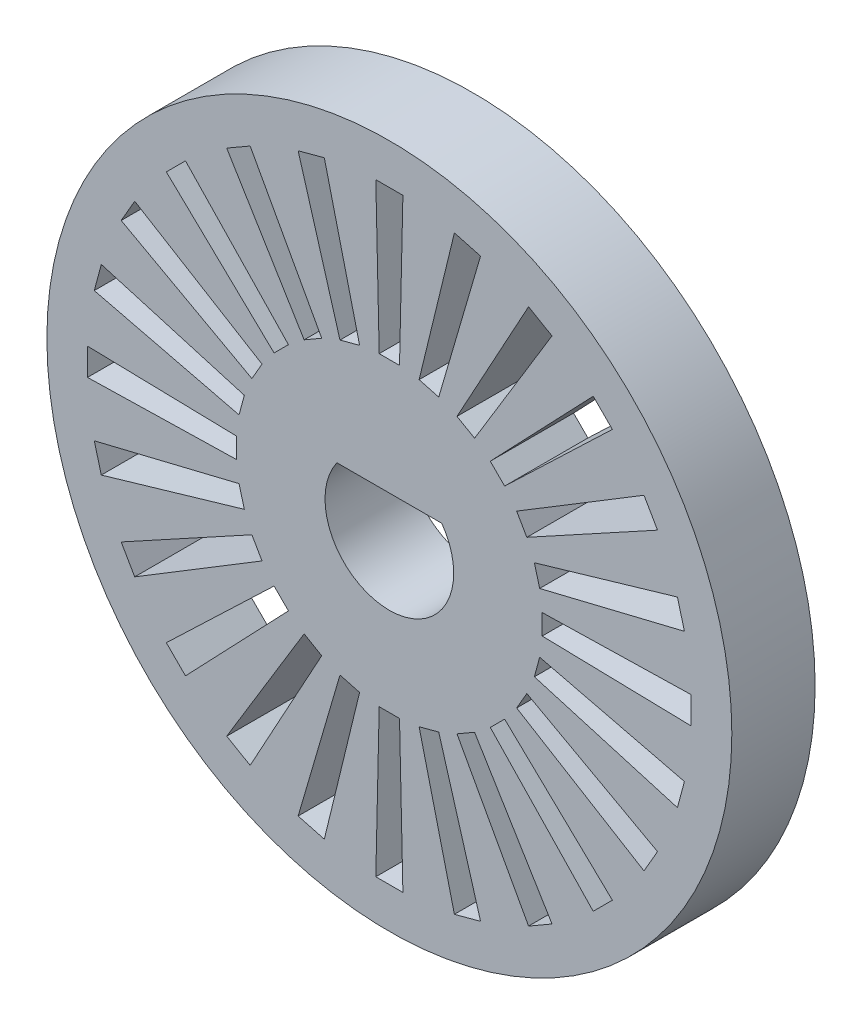
SolidWorks part; units mm, degrees
ref_plane "Alzado" through (0, 0, 0) normal (0, 0, 1) x (1, 0, 0)
ref_plane "Planta" through (0, 0, 0) normal (0, 1, 0) x (1, 0, 0)
ref_plane "Vista lateral" through (0, 0, 0) normal (1, 0, 0) x (0, 0, -1)
sketch "Croquis1" plane through (0, 0, 0) normal (0, 0, 1) x (1, 0, 0)
  line L0 (0, 12.8461) -> (0, 2.413) construction
  line L1 (0.508, 5.734) -> (-0.508, 5.734)
  line L2 (0.508, 5.734) -> (0.508, 11.3221)
  line L3 (0.508, 11.3221) -> (-0.508, 11.3221)
  line L4 (-0.508, 5.734) -> (-0.508, 11.3221)
  line L5 (0.508, 5.734) -> (-0.508, 11.3221) construction
  line L6 (0.508, 11.3221) -> (-0.508, 5.734) construction
  line L7 (-0.508, 11.3221) -> (-0.381, 5.734)
  line L8 (0.508, 11.3221) -> (0.381, 5.734)
  line L9 (3.4211, 10.8048) -> (1.8521, 5.4401)
  line L10 (2.4397, 11.0677) -> (1.1161, 5.6373)
  line L11 (3.4211, 10.8048) -> (2.4397, 11.0677)
  line L12 (1.9748, 5.4072) -> (0.9934, 5.6701)
  line L13 (6.101, 9.5512) -> (3.197, 4.7753)
  line L14 (5.2211, 10.0592) -> (2.5371, 5.1563)
  line L15 (6.101, 9.5512) -> (5.2211, 10.0592)
  line L16 (3.307, 4.7118) -> (2.4271, 5.2198)
  line L17 (8.3651, 7.6467) -> (4.324, 3.7852)
  line L18 (7.6467, 8.3651) -> (3.7852, 4.324)
  line L19 (8.3651, 7.6467) -> (7.6467, 8.3651)
  line L20 (4.4138, 3.6954) -> (3.6954, 4.4138)
  line L21 (10.0592, 5.2211) -> (5.1563, 2.5371)
  line L22 (9.5512, 6.101) -> (4.7753, 3.197)
  line L23 (10.0592, 5.2211) -> (9.5512, 6.101)
  line L24 (5.2198, 2.4271) -> (4.7118, 3.307)
  line L25 (11.0677, 2.4397) -> (5.6373, 1.1161)
  line L26 (10.8048, 3.4211) -> (5.4401, 1.8521)
  line L27 (11.0677, 2.4397) -> (10.8048, 3.4211)
  line L28 (5.6701, 0.9934) -> (5.4072, 1.9748)
  line L29 (11.3221, -0.508) -> (5.7341, -0.381)
  line L30 (11.3221, 0.508) -> (5.7341, 0.381)
  line L31 (11.3221, -0.508) -> (11.3221, 0.508)
  line L32 (5.7341, -0.508) -> (5.7341, 0.508)
  line L33 (10.8048, -3.4211) -> (5.4401, -1.8521)
  line L34 (11.0677, -2.4397) -> (5.6373, -1.1161)
  line L35 (10.8048, -3.4211) -> (11.0677, -2.4397)
  line L36 (5.4072, -1.9748) -> (5.6701, -0.9934)
  line L37 (9.5512, -6.101) -> (4.7753, -3.197)
  line L38 (10.0592, -5.2211) -> (5.1563, -2.5371)
  line L39 (9.5512, -6.101) -> (10.0592, -5.2211)
  line L40 (4.7118, -3.307) -> (5.2198, -2.4271)
  line L41 (7.6467, -8.3651) -> (3.7852, -4.324)
  line L42 (8.3651, -7.6467) -> (4.324, -3.7852)
  line L43 (7.6467, -8.3651) -> (8.3651, -7.6467)
  line L44 (3.6954, -4.4138) -> (4.4138, -3.6954)
  line L45 (5.2211, -10.0592) -> (2.5371, -5.1563)
  line L46 (6.101, -9.5512) -> (3.197, -4.7753)
  line L47 (5.2211, -10.0592) -> (6.101, -9.5512)
  line L48 (2.4271, -5.2198) -> (3.307, -4.7118)
  line L49 (2.4397, -11.0677) -> (1.1161, -5.6373)
  line L50 (3.4211, -10.8048) -> (1.8521, -5.4401)
  line L51 (2.4397, -11.0677) -> (3.4211, -10.8048)
  line L52 (0.9934, -5.6701) -> (1.9748, -5.4072)
  line L53 (-0.508, -11.3221) -> (-0.381, -5.7341)
  line L54 (0.508, -11.3221) -> (0.381, -5.7341)
  line L55 (-0.508, -11.3221) -> (0.508, -11.3221)
  line L56 (-0.508, -5.7341) -> (0.508, -5.7341)
  line L57 (-3.4211, -10.8048) -> (-1.8521, -5.4401)
  line L58 (-2.4397, -11.0677) -> (-1.1161, -5.6373)
  line L59 (-3.4211, -10.8048) -> (-2.4397, -11.0677)
  line L60 (-1.9748, -5.4072) -> (-0.9934, -5.6701)
  line L61 (-6.101, -9.5512) -> (-3.197, -4.7753)
  line L62 (-5.2211, -10.0592) -> (-2.5371, -5.1563)
  line L63 (-6.101, -9.5512) -> (-5.2211, -10.0592)
  line L64 (-3.307, -4.7118) -> (-2.4271, -5.2198)
  line L65 (-8.3651, -7.6467) -> (-4.324, -3.7852)
  line L66 (-7.6467, -8.3651) -> (-3.7852, -4.324)
  line L67 (-8.3651, -7.6467) -> (-7.6467, -8.3651)
  line L68 (-4.4138, -3.6954) -> (-3.6954, -4.4138)
  line L69 (-10.0592, -5.2211) -> (-5.1563, -2.5371)
  line L70 (-9.5512, -6.101) -> (-4.7753, -3.197)
  line L71 (-10.0592, -5.2211) -> (-9.5512, -6.101)
  line L72 (-5.2198, -2.4271) -> (-4.7118, -3.307)
  line L73 (-11.0677, -2.4397) -> (-5.6373, -1.1161)
  line L74 (-10.8048, -3.4211) -> (-5.4401, -1.8521)
  line L75 (-11.0677, -2.4397) -> (-10.8048, -3.4211)
  line L76 (-5.6701, -0.9934) -> (-5.4072, -1.9748)
  line L77 (-11.322, 0.508) -> (-5.734, 0.381)
  line L78 (-11.322, -0.508) -> (-5.734, -0.381)
  line L79 (-11.322, 0.508) -> (-11.322, -0.508)
  line L80 (-5.734, 0.508) -> (-5.734, -0.508)
  line L81 (-10.8048, 3.4211) -> (-5.4401, 1.8521)
  line L82 (-11.0677, 2.4397) -> (-5.6373, 1.1161)
  line L83 (-10.8048, 3.4211) -> (-11.0677, 2.4397)
  line L84 (-5.4072, 1.9748) -> (-5.6701, 0.9934)
  line L85 (-9.5512, 6.101) -> (-4.7753, 3.197)
  line L86 (-10.0592, 5.2211) -> (-5.1563, 2.5371)
  line L87 (-9.5512, 6.101) -> (-10.0592, 5.2211)
  line L88 (-4.7118, 3.307) -> (-5.2198, 2.4271)
  line L89 (-7.6467, 8.3651) -> (-3.7852, 4.324)
  line L90 (-8.3651, 7.6467) -> (-4.324, 3.7852)
  line L91 (-7.6467, 8.3651) -> (-8.3651, 7.6467)
  line L92 (-3.6954, 4.4138) -> (-4.4138, 3.6954)
  line L93 (-5.2211, 10.0592) -> (-2.5371, 5.1563)
  line L94 (-6.101, 9.5512) -> (-3.197, 4.7753)
  line L95 (-5.2211, 10.0592) -> (-6.101, 9.5512)
  line L96 (-2.4271, 5.2198) -> (-3.307, 4.7118)
  line L97 (-2.4397, 11.0677) -> (-1.1161, 5.6373)
  line L98 (-3.4211, 10.8048) -> (-1.8521, 5.4401)
  line L99 (-2.4397, 11.0677) -> (-3.4211, 10.8048)
  line L100 (-0.9934, 5.6701) -> (-1.9748, 5.4072)
  line L101 (-1.9675, 1.397) -> (1.9675, 1.397)
  circle A0 centre (0, 0) radius 2.413
  circle A1 centre (0, 0) radius 12.8461
  point P4 (0, 8.5281)
  point P15 (0, -2.413)
  point P154 (0, 2.413)
  point P155 (0, 0)
  point P156 (0, 8.5269)
  dimension "D1" = 4.826
  dimension "D2" = 25.6921
  dimension "D3" = 1.016
  dimension "D4" = 5.588
  dimension "D5" = 0.127
  dimension "D7" = 1.016
  dimension "D8" = 3.81
  dimension "D9" = 1.524
  dimension "D6" = 24
extrude "Saliente-Extruir2" add sketch "Croquis1" along normal blind 3.1242
